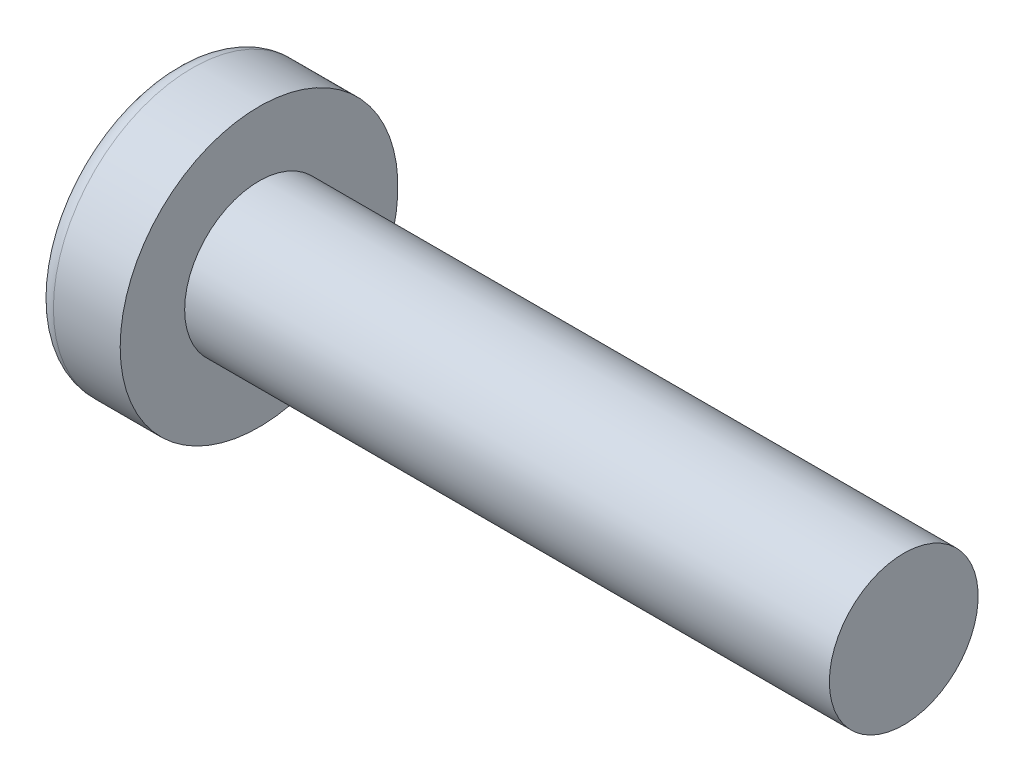
SolidWorks part; units mm, degrees
ref_plane "Plane1" through (0, 0, 0) normal (0, 0, 1) x (1, 0, 0)
ref_plane "Plane2" through (0, 0, 0) normal (0, 1, 0) x (1, 0, 0)
ref_plane "Plane3" through (0, 0, 0) normal (1, 0, 0) x (0, 0, -1)
sketch "BodySke" plane through (0, 0, 0) normal (0, 0, 1) x (1, 0, 0)
  line L0 (2.4, 1.5) -> (2.4, 2.8)
  line L1 (2.9, 6.35) -> (2.9, -3.175) construction
  line L2 (-25.4, 0) -> (127, 0) construction
  line L3 (15.4, 0) -> (0, 0)
  line L4 (2.4, 1.5) -> (15.4, 1.5)
  line L5 (15.4, 1.5) -> (15.4, 0)
  line L6 (1.0534, 2.8) -> (2.4, 2.8)
  line L7 (2.4, -1.5) -> (15.4, -1.5) construction
  line L8 (2.4, 6.35) -> (2.4, -3.175) construction
  arc A0 (0.7472, 2.6293) -> (0, 0) centre (5, 0) ccw
  arc A2 (0.7472, 2.6293) -> (1.0534, 2.8) centre (1.0534, 2.44) cw
  dimension "Head_fillet_rad" = 0.36
  dimension "Head_crown_rad" = 5
  dimension "Head_ht" = 2.4
  dimension "Diameter" = 3
  dimension "Length" = 13
  dimension "Head_dia" = 5.6
  dimension "Advance" = 0.5
  dimension "Thread_nom" = 13
revolve "Base-Revolve" add sketch "BodySke" angle 360 about L2
cosmetic thread "ThreadCosmetic" parameters "Thread_length"=12.5, "Thread_minor"=2.439
sketch "Sketch3" plane through (0, 0, 0) normal (1, 0, 0) x (0, 0, -1)
  line L0 (0.37, -1.45) -> (-0.37, -1.45)
  line L1 (0.37, -1.45) -> (0.37, 1.45)
  line L2 (-0.37, 1.45) -> (0.37, 1.45)
  line L3 (-0.37, 1.45) -> (-0.37, -1.45)
  dimension "D1" = 1.45
  dimension "Cross_dia" = 2.9
  dimension "D2" = 0.37
  dimension "Cross_width" = 0.74
ref_plane "Plane4" through (1.76, 0, 0) normal (1, 0, 0) x (0, 0, -1)
sketch "Sketch4" plane through (1.76, 0, 0) normal (1, 0, 0) x (0, 0, -1)
  line L0 (0.185, -0.185) -> (-0.185, -0.185)
  line L1 (0.185, -0.185) -> (0.185, 0.185)
  line L2 (-0.185, 0.185) -> (0.185, 0.185)
  line L3 (-0.185, 0.185) -> (-0.185, -0.185)
  dimension "D1" = 0.37
  dimension "D2" = 0.37
  dimension "D3" = 0.185
  dimension "D4" = 0.185
loft "Cut-Loft1" cut profiles "Sketch3", "Sketch4"
pattern_circular "CirPattern1" count 2 every 90 about axis through (0, 0, 0) along (1, 0, 0) of "Cut-Loft1"
sketch "ThdSchSke" plane through (0, 0, 0) normal (0, 0, 1) x (1, 0, 0)
  line L0 (2.9, -1.2195) -> (2.7036, -1.5)
  line L1 (2.9, -1.2195) -> (3.0964, -1.5)
  line L2 (3.0964, -1.5) -> (3.0964, -1.875)
  line L3 (-3.175, 0) -> (5.1513, 0) construction
  line L5 (3.0964, -1.875) -> (2.7036, -1.875)
  line L6 (2.7036, -1.875) -> (2.7036, -1.5)
  dimension "Thread_minor" = 2.439
  dimension "Diameter" = 3
  dimension "Start" = 2.9
  dimension "SideAngle" = 55
  dimension "VeeAngle" = 70
  dimension "Overcut" = 3.75
revolve "ThreadSchematic" [suppressed] cut sketch "ThdSchSke" angle 360 about L3
pattern_linear "ThdSchPat" [suppressed]
equation "\"D1@Sketch3\" = \"Cross_dia@Sketch3\" / 2"
equation "\"D2@Sketch3\" = \"Cross_width@Sketch3\" / 2"
equation "\"D1@Sketch4\" = \"Cross_width@Sketch3\" *.5"
equation "\"D2@Sketch4\" = \"D1@Sketch4\""
equation "\"D3@Sketch4\" = \"D1@Sketch4\" / 2"
equation "\"D4@Sketch4\" = \"D2@Sketch4\" / 2"
equation "\"Thread_length@ThreadCosmetic\" = ((sgn( (\"Length@BodySke\" - \"Advance@BodySke\" ) - \"Thread_nom@BodySke\" )-1)*( (\"Length@BodySke\" - \"Advance@BodySke\" ) - \"Thread_nom@BodySke\" ))/-2+ \"Thread_nom@BodySke\""
equation "\"Thread_minor@ThdSchSke\" = \"Thread_minor@ThreadCosmetic\""
equation "\"Diameter@ThdSchSke\" = \"Diameter@BodySke\""
equation "\"Overcut@ThdSchSke\" = \"Diameter@BodySke\" * 1.25"
equation "\"Start@ThdSchSke\" = \"Head_ht@BodySke\" + \"Length@BodySke\" - \"Thread_length@ThreadCosmetic\"  '---Non-countersunk---"
equation "\"Num_threads@ThdSchPat\" = int( \"Thread_length@ThreadCosmetic\" / \"Advance@BodySke\" + 0.999 )  + 1"
equation "\"Advance@ThdSchPat\" = \"Thread_length@ThreadCosmetic\" /  (\"Num_threads@ThdSchPat\" - 1) 'relax it"
